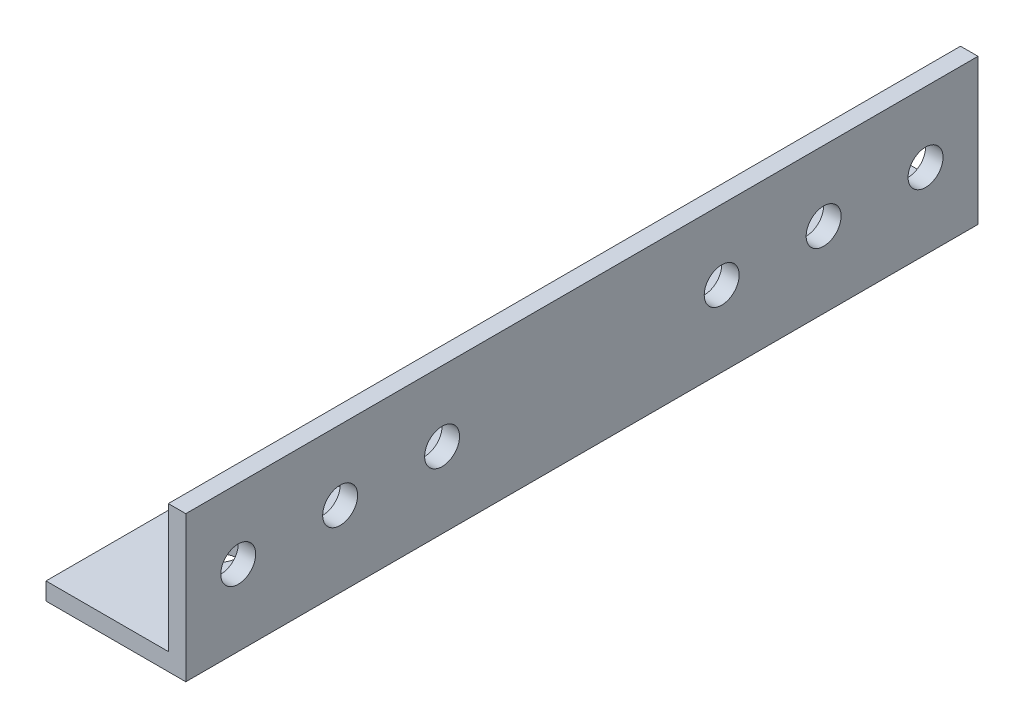
SolidWorks part; units mm, degrees
ref_plane "Alzado" through (0, 0, 0) normal (0, 0, 1) x (1, 0, 0)
ref_plane "Planta" through (0, 0, 0) normal (0, 1, 0) x (1, 0, 0)
ref_plane "Vista lateral" through (0, 0, 0) normal (1, 0, 0) x (0, 0, -1)
sketch "Croquis1" plane through (0, 0, 0) normal (0, 0, 1) x (1, 0, 0)
  line L0 (0, 0) -> (24, 0)
  line L1 (24, 0) -> (24, 25)
  line L2 (24, 25) -> (21, 25)
  line L3 (21, 25) -> (21, 3)
  line L4 (21, 3) -> (0, 3)
  line L5 (0, 3) -> (0, 0)
  dimension "D1" = 3
  dimension "D2" = 24
  dimension "D3" = 25
extrude "Saliente-Extruir1" add sketch "Croquis1" along normal blind 136
sketch "Croquis2" plane through (24, 0, 0) normal (1, 0, 0) x (0, 0, -1)
  line L0 (-127, 25) -> (-127, 13) construction
  line L1 (-136, 25) -> (0, 25) construction
  line L2 (-127, 13) -> (-136, 13) construction
  line L3 (-136, 0) -> (-136, 25) construction
  line L4 (-127, 13) -> (-109.5, 13) construction
  line L5 (-109.5, 13) -> (-92, 13) construction
  line L6 (-68, 0) -> (-68, 25) construction
  line L7 (-136, 0) -> (0, 0) construction
  circle A0 centre (-127, 13) radius 3
  circle A1 centre (-109.5, 13) radius 3
  circle A2 centre (-92, 13) radius 3
  circle A3 centre (-9, 13) radius 3
  circle A4 centre (-26.5, 13) radius 3
  circle A5 centre (-44, 13) radius 3
  dimension "D3" = 17.5
  dimension "D1" = 9
  dimension "D2" = 12
  dimension "D4" = 17.5
extrude "Cortar-Extruir1" cut sketch "Croquis2" against normal through all
sketch "Croquis3" plane through (0, 0, 0) normal (0, -1, 0) x (1, 0, 0)
  line L0 (24, 19.8) -> (10, 19.8) construction
  line L1 (24, 136) -> (24, 0) construction
  line L2 (10, 19.8) -> (10, 0) construction
  line L3 (0, 0) -> (24, 0) construction
  line L4 (10, 19.8) -> (10, 42) construction
  line L5 (24, 68) -> (0, 68) construction
  line L6 (0, 136) -> (0, 0) construction
  circle A0 centre (10, 19.8) radius 3
  circle A1 centre (10, 42) radius 3
  circle A2 centre (10, 116.2) radius 3
  circle A3 centre (10, 94) radius 3
  dimension "D3" = 22.2
  dimension "D1" = 19.8
  dimension "D2" = 14
extrude "Cortar-Extruir2" cut sketch "Croquis3" against normal through all
